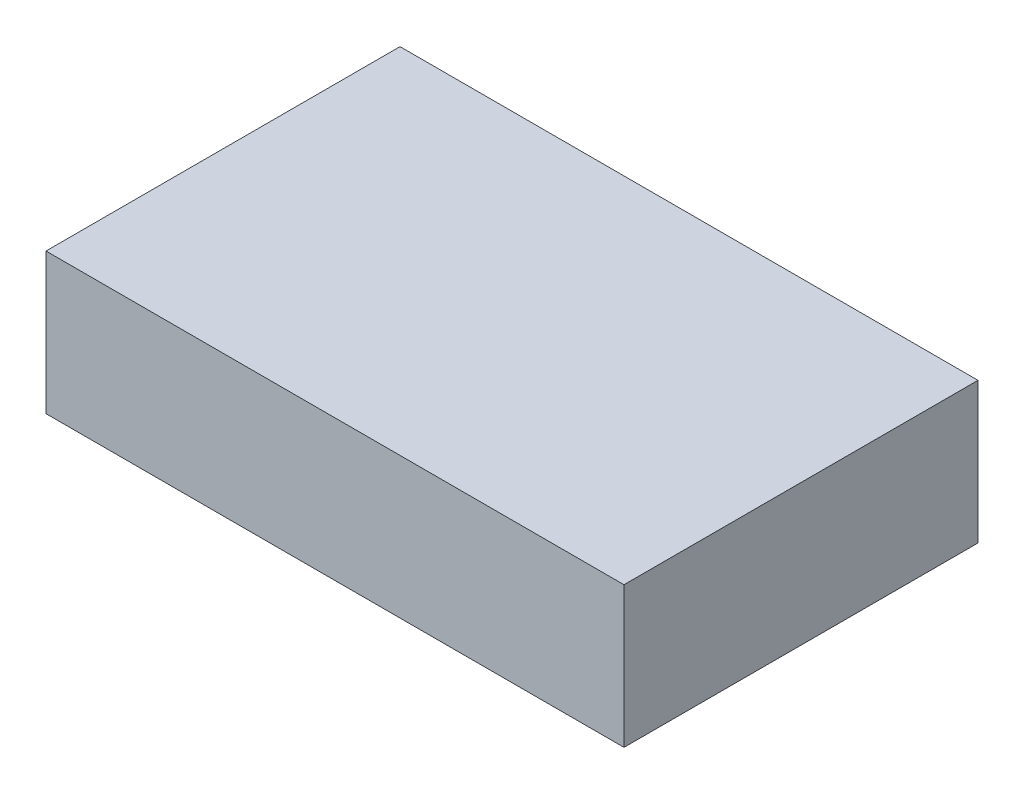
SolidWorks part; units mm, degrees
ref_plane "Front Plane" through (0, 0, 0) normal (0, 0, 1) x (1, 0, 0)
ref_plane "Top Plane" through (0, 0, 0) normal (0, 1, 0) x (1, 0, 0)
ref_plane "Right Plane" through (0, 0, 0) normal (1, 0, 0) x (0, 0, -1)
sketch "Sketch1" plane through (0, 0, 0) normal (0, 1, 0) x (1, 0, 0)
  line L1 (-80, -49) -> (80, -49)
  line L2 (-80, -49) -> (-80, 49)
  line L3 (-80, 49) -> (80, 49)
  line L4 (80, -49) -> (80, 49)
  line L5 (-80, -49) -> (80, 49) construction
  line L6 (-80, 49) -> (80, -49) construction
  point P0 (0, 0)
  dimension "D1" = 98
  dimension "D2" = 160
extrude "Boss-Extrude1" add sketch "Sketch1" along normal blind 39
hole_wizard "M3 Clearance Hole1" positions "Sketch2" profile "Sketch4" hole size "M3" standard "ANSI Metric"
sketch "Sketch2" plane through (0, 0, 0) normal (0, -1, 0) x (-1, 0, 0)
  line L0 (80, 49) -> (80, -49) construction
  line L1 (80, -49) -> (-80, -49) construction
  line L2 (-80, -49) -> (-80, 49) construction
  line L3 (-80, 49) -> (80, 49) construction
  point P0 (-75, 44)
  point P2 (77, -43)
  dimension "D1" = 3
  dimension "D2" = 6
  dimension "D3" = 5
  dimension "D4" = 5
sketch "Sketch4" plane through (75, 0, -44) normal (1, 0, 0) x (0, 0, -1)
  line L0 (0, 0) -> (0, 21.0815)
  line L1 (0, 21.0815) -> (1.8, 20)
  line L2 (1.8, 20) -> (1.8, 0)
  line L5 (1.8, 0) -> (0, 0)
  line L10 (0, 21.0815) -> (-1.8, 20) construction
  line L11 (0, -6.35) -> (0, 107.95) construction
  dimension "Hole Dia." = 3.6
  dimension "Hole Depth" = 20
  dimension "Drill Angle" = 118
